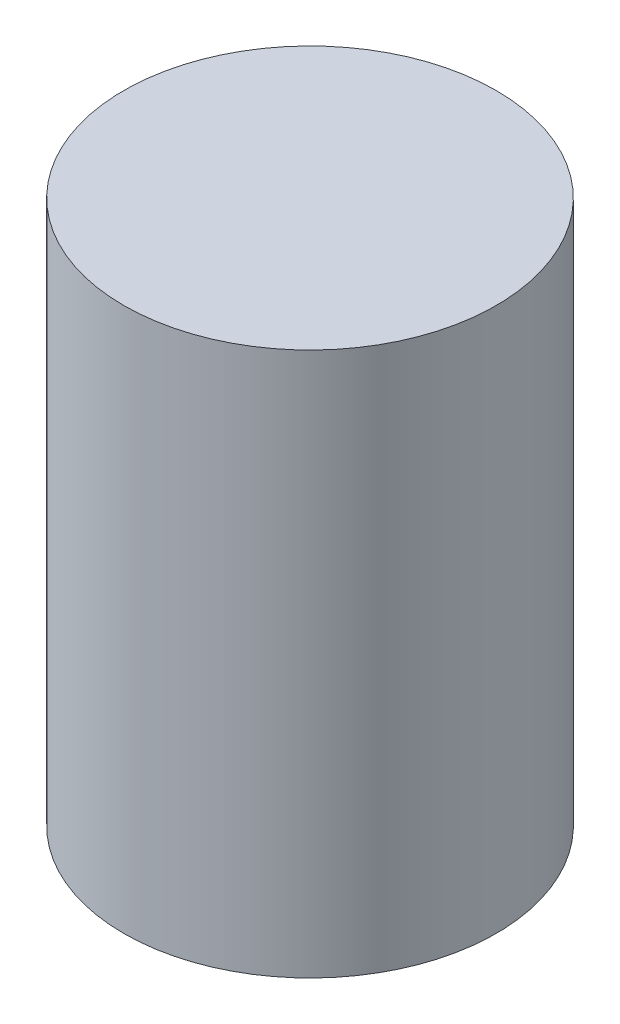
SolidWorks part; units mm, degrees
material "Galvanized Steel"
ref_plane "Front Plane" through (0, 0, 0) normal (0, 0, 1) x (1, 0, 0)
ref_plane "Top Plane" through (0, 0, 0) normal (0, 1, 0) x (1, 0, 0)
ref_plane "Right Plane" through (0, 0, 0) normal (1, 0, 0) x (0, 0, -1)
sketch "Sketch1" plane through (0, 0, 0) normal (0, 1, 0) x (1, 0, 0)
  circle A0 centre (0, 0) radius 15.75
  dimension "D1" = 31.5
extrude "Boss-Extrude1" add sketch "Sketch1" along normal blind 46
